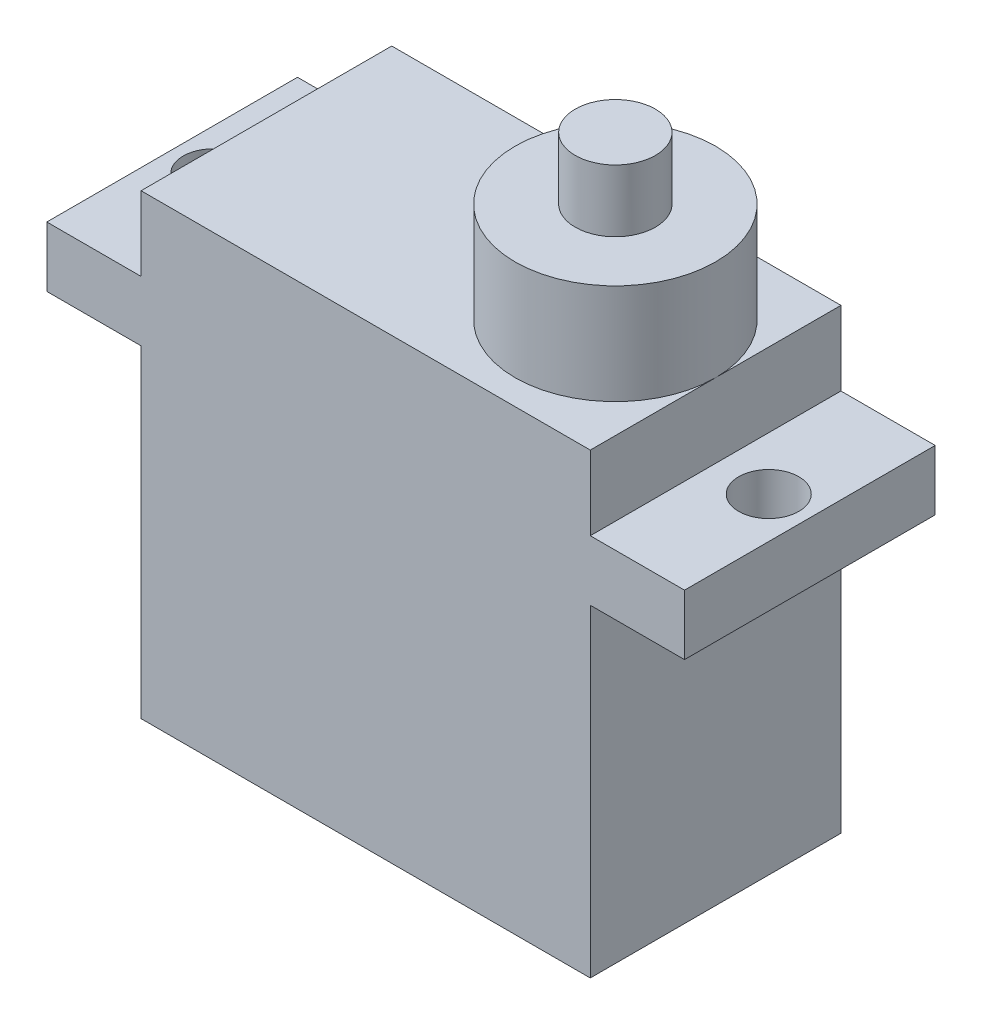
SolidWorks part; units mm, degrees
ref_plane "前视基准面" through (0, 0, 0) normal (0, 0, 1) x (1, 0, 0)
ref_plane "上视基准面" through (0, 0, 0) normal (0, 1, 0) x (1, 0, 0)
ref_plane "右视基准面" through (0, 0, 0) normal (1, 0, 0) x (0, 0, -1)
sketch "草图1" plane through (0, 0, 0) normal (0, 1, 0) x (1, 0, 0)
  line L1 (-11.2, 6.25) -> (11.2, 6.25)
  line L2 (-11.2, 6.25) -> (-11.2, -6.25)
  line L3 (-11.2, -6.25) -> (11.2, -6.25)
  line L4 (11.2, 6.25) -> (11.2, -6.25)
  line L5 (-11.2, 6.25) -> (11.2, -6.25) construction
  line L6 (-11.2, -6.25) -> (11.2, 6.25) construction
  point P0 (0, 0)
  dimension "D1" = 12.5
  dimension "D2" = 22.4
extrude "凸台-拉伸1" add sketch "草图1" along normal blind 16.1
sketch "草图2" plane through (0, 16.1, 0) normal (0, 1, 0) x (1, 0, 0)
  line L0 (-11.2, -6.25) -> (11.2, -6.25) construction
  line L1 (-15.9, 6.25) -> (15.9, 6.25)
  line L2 (-15.9, 6.25) -> (-15.9, -6.25)
  line L3 (-15.9, -6.25) -> (15.9, -6.25)
  line L4 (15.9, 6.25) -> (15.9, -6.25)
  line L5 (-15.9, 6.25) -> (15.9, -6.25) construction
  line L6 (-15.9, -6.25) -> (15.9, 6.25) construction
  line L7 (-13.85, 0) -> (13.85, 0) construction
  circle A0 centre (13.85, 0) radius 1.5
  circle A1 centre (-13.85, 0) radius 1.5
  point P0 (0, 0)
  point P11 (0, 0)
  dimension "D3" = 3
  dimension "D4" = 3
  dimension "D1" = 31.8
  dimension "D2" = 27.7
extrude "凸台-拉伸2" add sketch "草图2" along normal blind 3
sketch "草图3" plane through (0, 0, 0) normal (0, -1, 0) x (1, 0, 0)
  line L1 (-11.2, 6.25) -> (11.2, 6.25)
  line L2 (-11.2, 6.25) -> (-11.2, -6.25)
  line L3 (-11.2, -6.25) -> (11.2, -6.25)
  line L4 (11.2, 6.25) -> (11.2, -6.25)
extrude "凸台-拉伸3" add sketch "草图3" against normal blind 22.8
sketch "草图4" plane through (0, 22.8, 0) normal (0, 1, 0) x (1, 0, 0)
  line L0 (11.2, 6.25) -> (11.2, -6.25) construction
  circle A0 centre (6.2, 0) radius 5
  point P4 (0, 0)
  point P6 (0, 0)
  dimension "D1" = 10
extrude "凸台-拉伸4" add sketch "草图4" along normal blind 5
sketch "草图5" plane through (0, 0, 0) normal (0, -1, 0) x (1, 0, 0)
  circle A0 centre (6.2, 0) radius 2
  dimension "D1" = 4
extrude "凸台-拉伸5" add sketch "草图5" against normal blind 30.9
